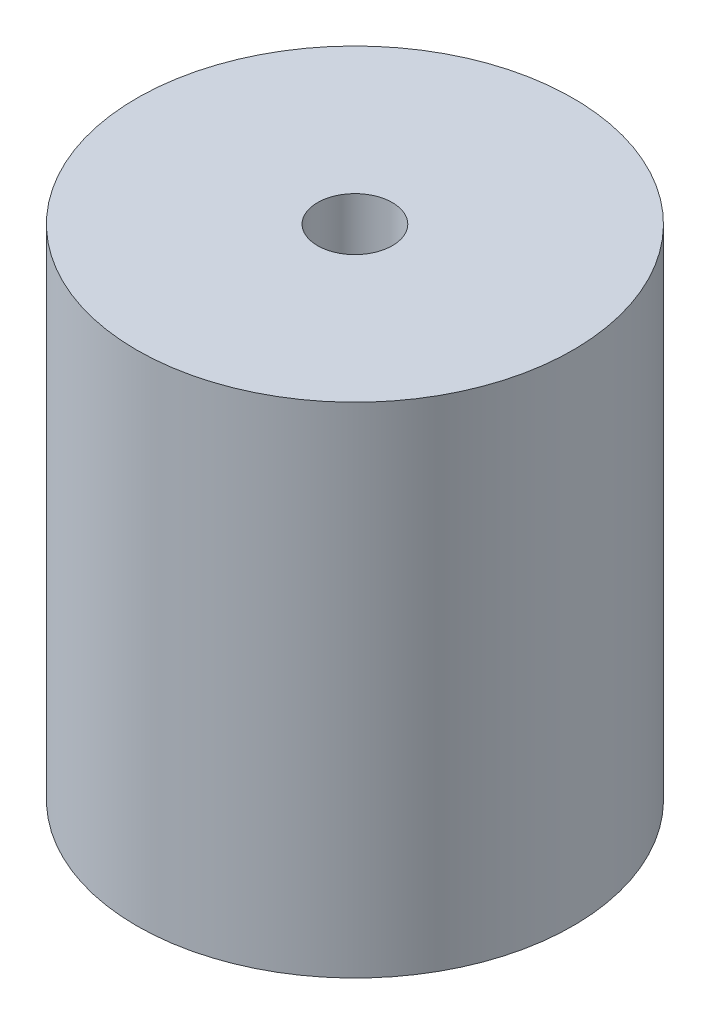
SolidWorks part; units mm, degrees
material "Alloy Steel"
ref_plane "Front Plane" through (0, 0, 0) normal (0, 0, 1) x (1, 0, 0)
ref_plane "Top Plane" through (0, 0, 0) normal (0, 1, 0) x (1, 0, 0)
ref_plane "Right Plane" through (0, 0, 0) normal (1, 0, 0) x (0, 0, -1)
sketch "Sketch1" plane through (0, 0, 0) normal (0, 1, 0) x (1, 0, 0)
  circle A0 centre (0, 0) radius 175
  dimension "D1" = 350
extrude "Boss-Extrude1" add sketch "Sketch1" along normal blind 400
scale "Scale1" bodies to scale 103 scale about centroid uniform scaling yes scale factor 0.1
sketch "Sketch3" plane through (0, 220, 0) normal (0, 1, 0) x (1, 0, 0)
  circle A0 centre (0, 0) radius 3
  dimension "D1" = 6
extrude "Cut-Extrude1" cut sketch "Sketch3" against normal through all
